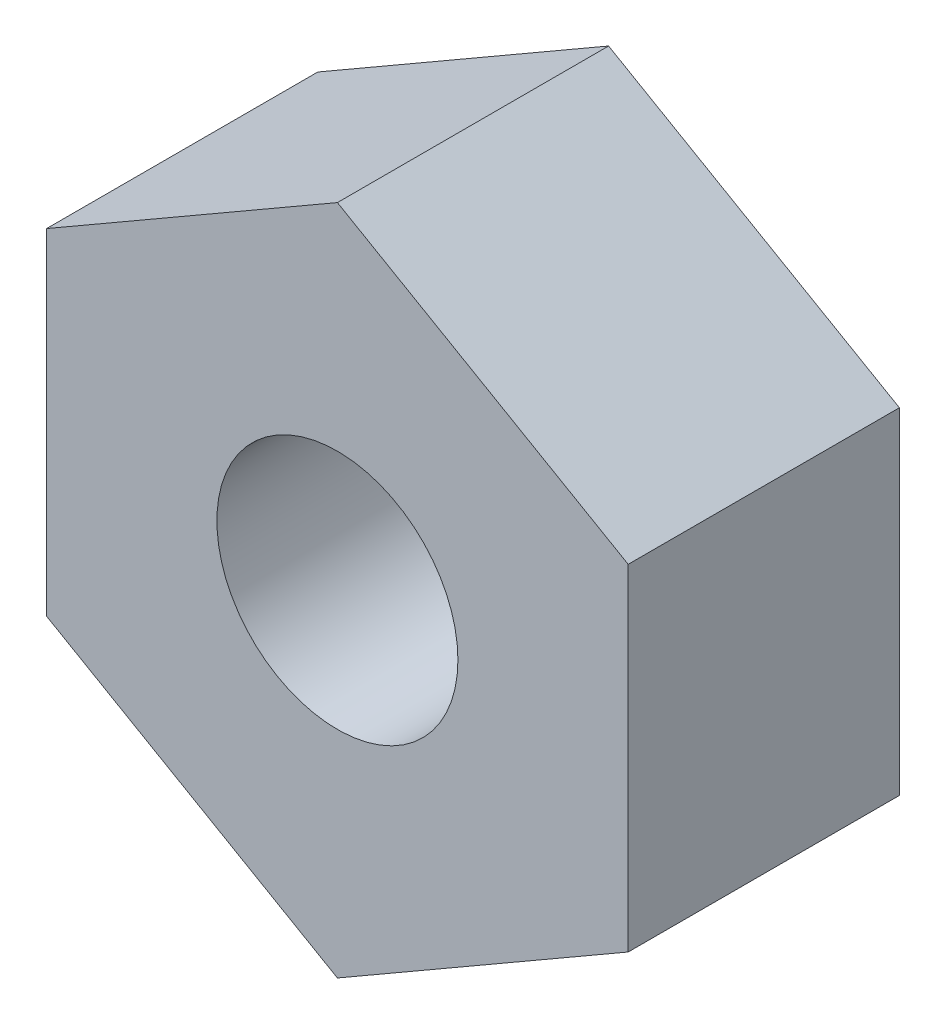
SolidWorks part; units mm, degrees
ref_plane "Front Plane" through (0, 0, 0) normal (0, 0, 1) x (1, 0, 0)
ref_plane "Top Plane" through (0, 0, 0) normal (0, 1, 0) x (1, 0, 0)
ref_plane "Right Plane" through (0, 0, 0) normal (1, 0, 0) x (0, 0, -1)
sketch "Sketch1" plane through (0, 0, 0) normal (0, 0, 1) x (1, 0, 0)
  line L1 (0, 11.1429) -> (-9.65, 5.5714)
  line L2 (-9.65, 5.5714) -> (-9.65, -5.5714)
  line L3 (-9.65, -5.5714) -> (0, -11.1429)
  line L4 (0, -11.1429) -> (9.65, -5.5714)
  line L5 (9.65, -5.5714) -> (9.65, 5.5714)
  line L6 (9.65, 5.5714) -> (0, 11.1429)
  circle A0 centre (0, 0) radius 9.65 construction
  circle A1 centre (0, 0) radius 4
  point P10 (0, 0)
  dimension "D2" = 8
  dimension "D1" = 19.3
extrude "Boss-Extrude1" add sketch "Sketch1" along normal mid plane 9
